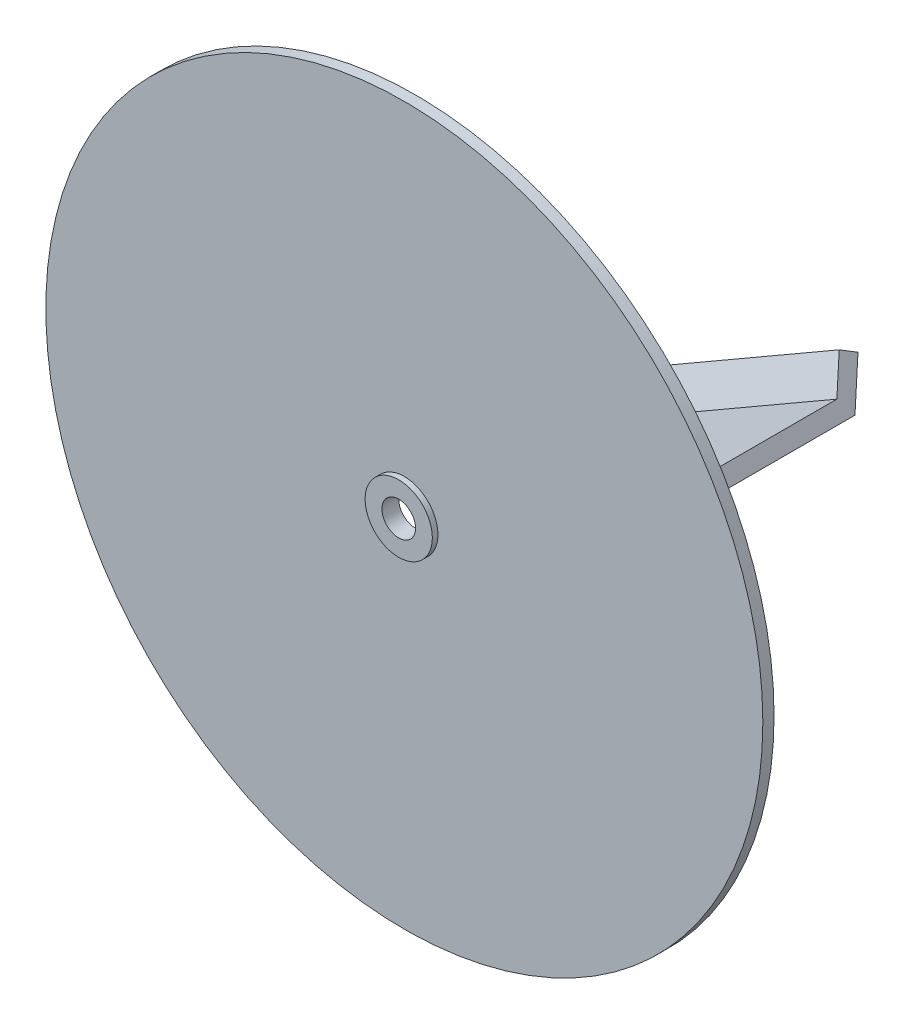
SolidWorks part; units mm, degrees
material "Plain Carbon Steel"
ref_plane "Front Plane" through (0, 0, 0) normal (0, 0, 1) x (1, 0, 0)
ref_plane "Top Plane" through (0, 0, 0) normal (0, 1, 0) x (1, 0, 0)
ref_plane "Right Plane" through (0, 0, 0) normal (1, 0, 0) x (0, 0, -1)
sketch "Sketch1" plane through (0, 0, 0) normal (0, 0, 1) x (1, 0, 0)
  circle A0 centre (0, 0) radius 203.2
  circle A1 centre (0, 0) radius 9.525
  dimension "D1" = 406.4
  dimension "D2" = 19.05
extrude "Boss-Extrude1" add sketch "Sketch1" along normal blind 6.35
ref_plane "Plane1" through (0, -25.4, 0) normal (0, 1, 0) x (1, 0, 0)
sketch "Sketch2" plane through (0, -25.4, 0) normal (0, 1, 0) x (1, 0, 0)
  line L0 (-4.7625, 0) -> (-4.7625, 76.2)
  line L1 (203.2, 0) -> (-203.2, 0) construction
  line L2 (-4.7625, 76.2) -> (17.2345, 88.9)
  line L3 (17.2345, 88.9) -> (21.997, 80.6511)
  line L4 (21.997, 80.6511) -> (4.7625, 70.7007)
  line L5 (4.7625, 70.7007) -> (4.7625, 0)
  line L6 (4.7625, 0) -> (-4.7625, 0)
  point P4 (0, 0)
  dimension "D1" = 9.525
  dimension "D2" = 76.2
  dimension "D3" = 120
  dimension "D4" = 25.4
extrude "Boss-Extrude2" add sketch "Sketch2" against normal blind 171.45
pattern_circular "CirPattern1" count 3 every 120 about axis through (0, 0, 0) along (0, 0, 1) of "Boss-Extrude2"
sketch "Sketch3" plane through (0, 0, 6.35) normal (0, 0, 1) x (1, 0, 0)
  circle A0 centre (0, 0) radius 9.525
  circle A1 centre (0, 0) radius 19.05
  circle A2 centre (0, 0) radius 9.525 construction
  dimension "D1" = 38.1
extrude "Boss-Extrude3" add sketch "Sketch3" along normal blind 3.175
